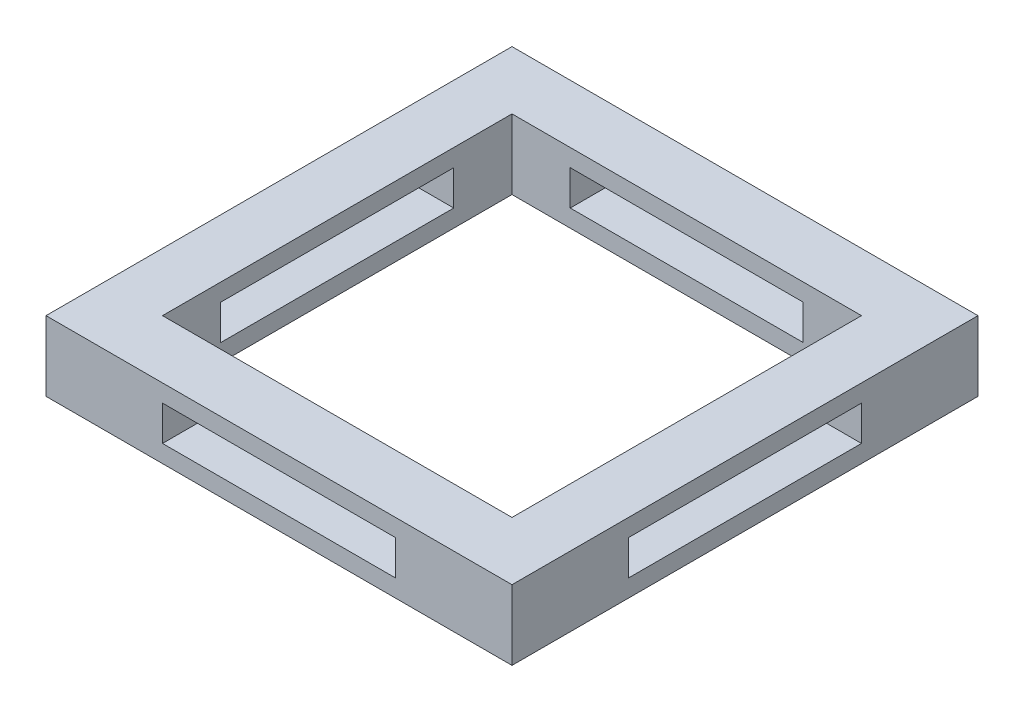
SolidWorks part; units mm, degrees
ref_plane "Front Plane" through (0, 0, 0) normal (0, 0, 1) x (1, 0, 0)
ref_plane "Top Plane" through (0, 0, 0) normal (0, 1, 0) x (1, 0, 0)
ref_plane "Right Plane" through (0, 0, 0) normal (1, 0, 0) x (0, 0, -1)
sketch "Sketch1" plane through (0, 0, 0) normal (0, 1, 0) x (1, 0, 0)
  line L1 (10, -10) -> (-10, -10)
  line L2 (10, -10) -> (10, 10)
  line L3 (10, 10) -> (-10, 10)
  line L4 (-10, -10) -> (-10, 10)
  line L5 (7.5, -7.5) -> (-7.5, -7.5)
  line L6 (7.5, -7.5) -> (7.5, 7.5)
  line L7 (7.5, 7.5) -> (-7.5, 7.5)
  line L8 (-7.5, -7.5) -> (-7.5, 7.5)
  line L9 (0, 7.5) -> (0, -7.5) construction
  line L10 (7.5, 0) -> (-7.5, 0) construction
  point P0 (0, 0)
  point P4 (0, 0)
  dimension "D1" = 20
  dimension "D2" = 20
  dimension "D3" = 15
  dimension "D4" = 15
  dimension "D5" = 2.5
extrude "Boss-Extrude1" add sketch "Sketch1" along normal blind 3
sketch "Sketch2" plane through (0, 0, 10) normal (0, 0, 1) x (1, 0, 0)
  line L0 (-10, 3) -> (-10, 0) construction
  line L1 (5, 0.75) -> (-5, 0.75)
  line L2 (5, 0.75) -> (5, 2.25)
  line L3 (5, 2.25) -> (-5, 2.25)
  line L4 (-5, 0.75) -> (-5, 2.25)
  line L5 (0, 2.25) -> (0, 0.75) construction
  line L6 (5, 1.5) -> (-5, 1.5) construction
  line L7 (-10, 0) -> (10, 0) construction
  point P0 (0, 1.5)
  dimension "D1" = 5
  dimension "D2" = 0.75
  dimension "D3" = 1.5
  dimension "D4" = 10
extrude "Cut-Extrude1" cut sketch "Sketch2" against normal through all
sketch "Sketch3" plane through (-10, 0, 0) normal (-1, 0, 0) x (0, 0, 1)
  line L0 (-10, 3) -> (-10, 0) construction
  line L1 (5, 0.75) -> (-5, 0.75)
  line L2 (5, 0.75) -> (5, 2.25)
  line L3 (5, 2.25) -> (-5, 2.25)
  line L4 (-5, 0.75) -> (-5, 2.25)
  line L5 (0, 2.25) -> (0, 0.75) construction
  line L6 (5, 1.5) -> (-5, 1.5) construction
  line L7 (-10, 0) -> (10, 0) construction
  point P0 (0, 1.5)
  dimension "D1" = 1.5
  dimension "D2" = 10
  dimension "D3" = 5
  dimension "D4" = 0.75
extrude "Cut-Extrude2" cut sketch "Sketch3" against normal through all
